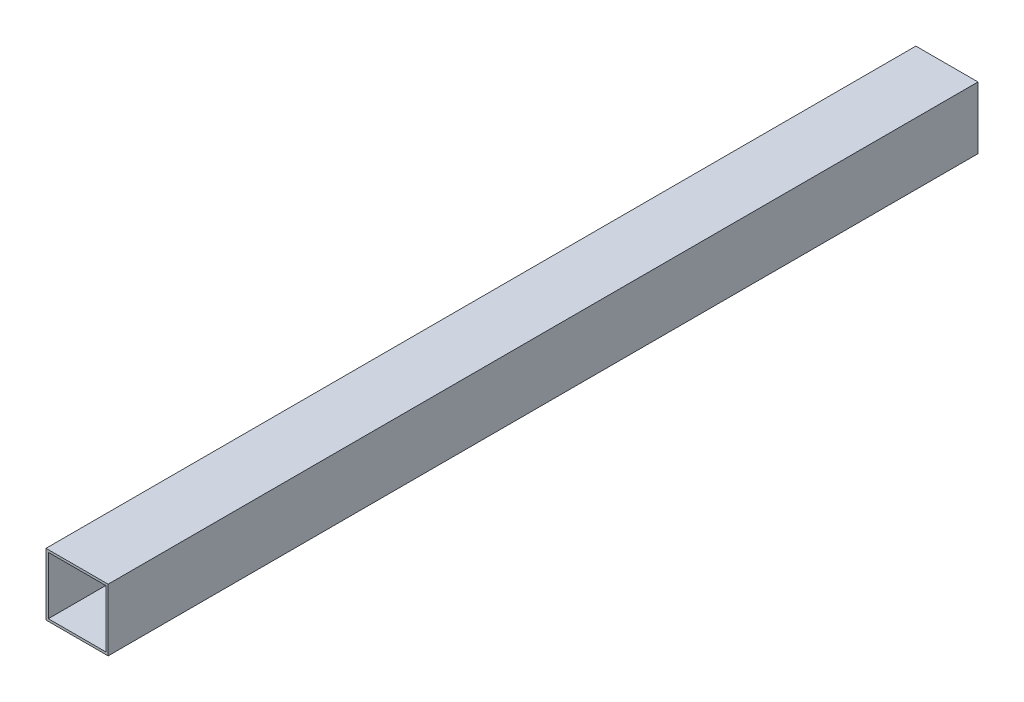
SolidWorks part; units mm, degrees
ref_plane "Plan de face" through (0, 0, 0) normal (0, 0, 1) x (1, 0, 0)
ref_plane "Plan de dessus" through (0, 0, 0) normal (0, 1, 0) x (1, 0, 0)
ref_plane "Plan de droite" through (0, 0, 0) normal (1, 0, 0) x (0, 0, -1)
sketch "Esquisse1" plane through (0, 0, 0) normal (0, 0, 1) x (1, 0, 0)
  line L1 (-20, -20) -> (20, -20)
  line L2 (-20, -20) -> (-20, 20)
  line L3 (-20, 20) -> (20, 20)
  line L4 (20, -20) -> (20, 20)
  line L5 (-20, -20) -> (20, 20) construction
  line L6 (-20, 20) -> (20, -20) construction
  line L7 (-18.5, -18.5) -> (18.5, -18.5)
  line L8 (-18.5, -18.5) -> (-18.5, 18.5)
  line L9 (-18.5, 18.5) -> (18.5, 18.5)
  line L10 (18.5, -18.5) -> (18.5, 18.5)
  line L11 (-18.5, -18.5) -> (18.5, 18.5) construction
  line L12 (-18.5, 18.5) -> (18.5, -18.5) construction
  point P0 (0, 0)
  point P6 (0, 0)
  dimension "D1" = 40
  dimension "D2" = 40
  dimension "D3" = 37
  dimension "D4" = 37
extrude "Boss.-Extru.1" add sketch "Esquisse1" along normal blind 560
